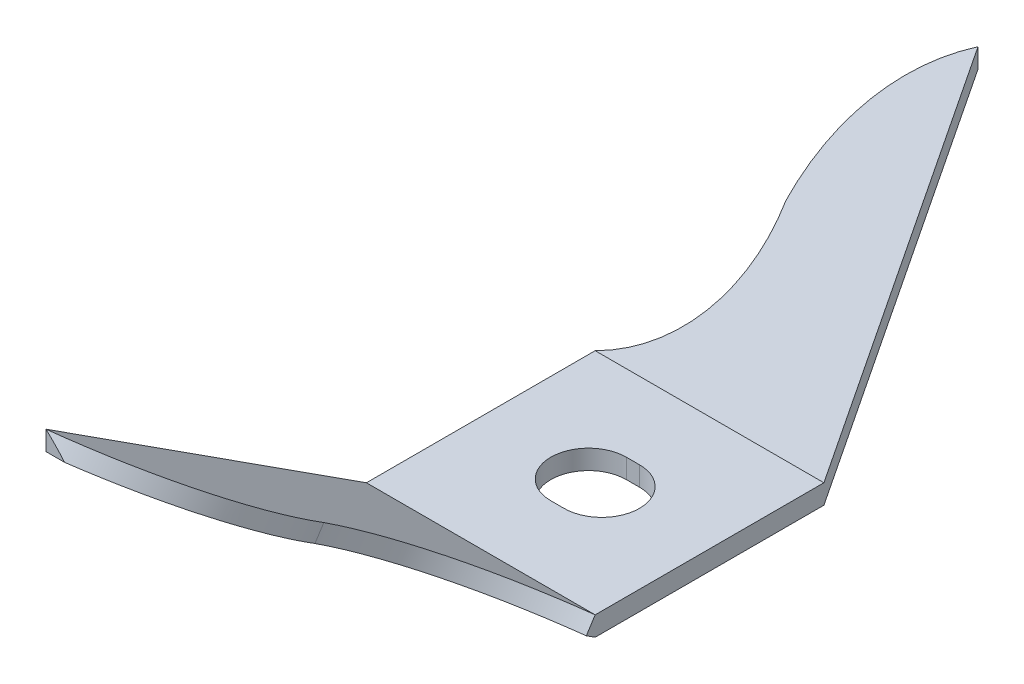
SolidWorks part; units mm, degrees
ref_plane "Front Plane" through (0, 0, 0) normal (0, 0, 1) x (1, 0, 0)
ref_plane "Top Plane" through (0, 0, 0) normal (0, 1, 0) x (1, 0, 0)
ref_plane "Right Plane" through (0, 0, 0) normal (1, 0, 0) x (0, 0, -1)
sketch "Sketch1" plane through (0, 0, 0) normal (0, 1, 0) x (1, 0, 0)
  line L0 (-0.4394, 0) -> (0.4394, 0) construction
  line L1 (-0.4394, 2.5146) -> (0.4394, 2.5146)
  line L2 (-0.4394, -2.5146) -> (0.4394, -2.5146)
  line L4 (-7.62, -7.62) -> (7.62, -7.62)
  line L5 (-7.62, -7.62) -> (-7.62, 7.62)
  line L6 (-7.62, 7.62) -> (7.62, 7.62)
  line L7 (7.62, -7.62) -> (7.62, 7.62)
  line L8 (-7.62, -7.62) -> (7.62, 7.62) construction
  line L9 (-7.62, 7.62) -> (7.62, -7.62) construction
  arc A0 (-0.4394, 2.5146) -> (-0.4394, -2.5146) centre (-0.4394, 0) ccw
  arc A1 (0.4394, -2.5146) -> (0.4394, 2.5146) centre (0.4394, 0) ccw
  point P2 (0, 0)
  point P8 (-2.954, 0)
  point P9 (0, 0)
  dimension "D1" = 5.0292
  dimension "D2" = 2.954
  dimension "D3" = 15.24
extrude "Boss-Extrude1" add sketch "Sketch1" along normal blind 1.2954
sketch "Sketch3" plane through (-7.62, 0, 0) normal (-1, 0, 0) x (0, 0, 1)
  line L0 (7.62, 1.2954) -> (28.9674, 15.0595)
  line L2 (7.62, 0) -> (28.9674, 13.7641)
  line L3 (28.9674, 15.0595) -> (28.9674, 13.7641)
  line L4 (7.62, 1.2954) -> (7.62, 0)
  line L5 (-7.62, 1.2954) -> (-17.8856, 21.3211)
  line L6 (-7.62, 0) -> (-17.8856, 20.0257)
  line L7 (-17.8856, 21.3211) -> (-17.8856, 20.0257)
  line L8 (-7.62, 1.2954) -> (-7.62, 0)
  dimension "D1" = 25.4
  dimension "D2" = 13.7641
  dimension "D3" = 10.2656
  dimension "D4" = 20.0257
extrude "Boss-Extrude2" add sketch "Sketch3" against normal blind 15.24
sketch "Sketch4" plane through (0, -2.5554, 1.6476) normal (0, 0.8404, -0.5419) x (1, 0, 0)
  line L0 (7.62, -7.1062) -> (7.62, -32.5062)
  line L1 (7.62, -32.5062) -> (-7.62, -32.5062)
  arc A0 (-7.62, -32.5062) -> (0, -19.5484) centre (-13.8086, -20.1475) ccw
  arc A1 (0, -19.5484) -> (7.62, -7.1062) centre (14.4034, -19.815) cw
  dimension "D1" = 13.8215
  dimension "D2" = 14.4058
  dimension "D3" = 12.7088
  dimension "D4" = 13.0413
extrude "Cut-Extrude1" cut sketch "Sketch4" against normal blind 15.24
sketch "Sketch5" plane through (0, -2.8237, -5.5084) normal (0, 0.4562, 0.8899) x (1, 0, 0)
  line L0 (-7.62, 4.6288) -> (-7.62, 27.1324)
  line L1 (-7.62, 27.1324) -> (7.62, 27.1324)
  arc A0 (7.62, 27.1324) -> (0, 15.7979) centre (17.4783, 12.2762) ccw
  arc A1 (0, 15.7979) -> (-7.62, 4.6288) centre (-12.8525, 16.3825) cw
  dimension "D3" = 12.8658
  dimension "D4" = 17.8296
  dimension "D1" = 11.7537
  dimension "D2" = 7.6473
extrude "Cut-Extrude2" cut sketch "Sketch5" against normal blind 15.24
